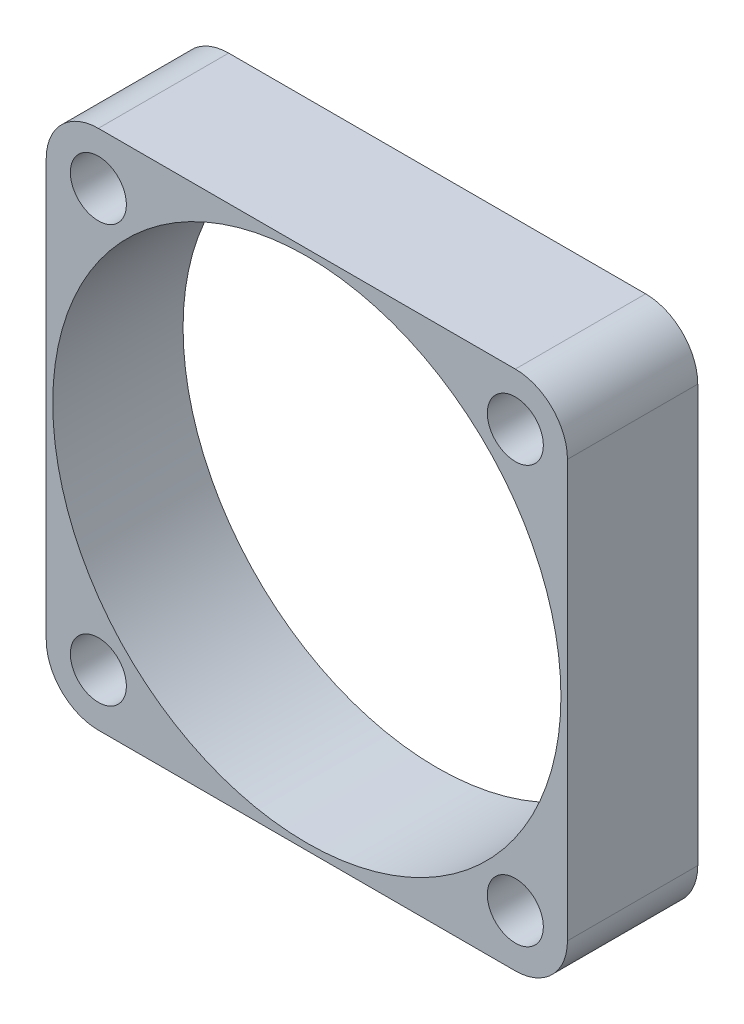
SolidWorks part; units mm, degrees
ref_plane "Front" through (0, 0, 0) normal (0, 0, 1) x (1, 0, 0)
ref_plane "Top" through (0, 0, 0) normal (0, 1, 0) x (1, 0, 0)
ref_plane "Right" through (0, 0, 0) normal (1, 0, 0) x (0, 0, -1)
sketch "Sketch1" plane through (0, 0, 0) normal (0, 0, 1) x (1, 0, 0)
  line L1 (4, 0) -> (36, 0)
  line L2 (0, -4) -> (0, -36)
  line L3 (4, -40) -> (36, -40)
  line L4 (40, -4) -> (40, -36)
  arc A0 (36, 0) -> (40, -4) centre (36, -4) cw
  arc A1 (36, -40) -> (40, -36) centre (36, -36) ccw
  arc A2 (0, -4) -> (4, 0) centre (4, -4) cw
  arc A3 (4, -40) -> (0, -36) centre (4, -36) cw
  point P10 (0, 0)
  dimension "D3" = 4
  dimension "D4" = 4
  dimension "D1" = 40
  dimension "D2" = 40
extrude "Extrude1" add sketch "Sketch1" along normal blind 10
sketch "Sketch2" plane through (0, 0, 10) normal (0, 0, 1) x (1, 0, 0)
  line L0 (40, -36) -> (40, -4) construction
  line L1 (36, 0) -> (4, 0) construction
  circle A0 centre (20, -20) radius 19.5
  dimension "D3" = 39
  dimension "D1" = 20
  dimension "D2" = 20
extrude "Cut-Extrude1" cut sketch "Sketch2" against normal blind 20
sketch "Sketch4" plane through (0, 0, 10) normal (0, 0, 1) x (1, 0, 0)
  line L0 (40, -36) -> (40, -4) construction
  line L1 (36, 0) -> (4, 0) construction
  line L2 (0, -4) -> (0, -36) construction
  line L3 (4, -40) -> (36, -40) construction
  circle A1 centre (36, -4) radius 2.15
  circle A2 centre (4, -4) radius 2.15
  circle A3 centre (4, -36) radius 2.15
  circle A4 centre (36, -36) radius 2.15
  dimension "D1" = 4.3
  dimension "D2" = 4.3
  dimension "D3" = 4.3
  dimension "D4" = 4.3
  dimension "D5" = 4
  dimension "D6" = 4
  dimension "D7" = 4
  dimension "D8" = 4
extrude "Cut-Extrude2" cut sketch "Sketch4" against normal blind 20
